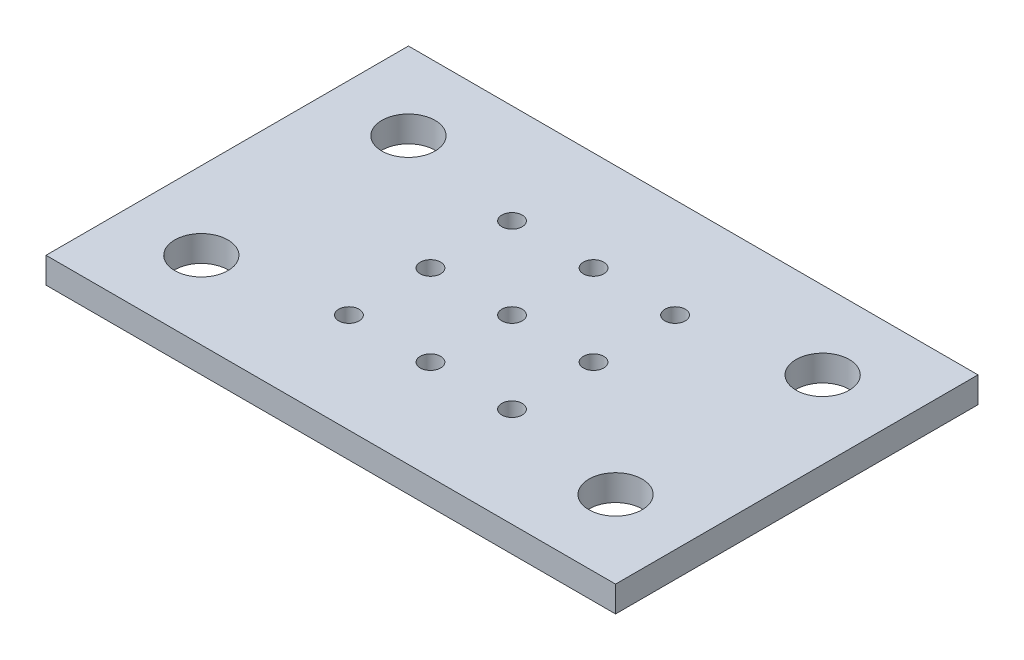
SolidWorks part; units mm, degrees
ref_plane "Front Plane" through (0, 0, 0) normal (0, 0, 1) x (1, 0, 0)
ref_plane "Top Plane" through (0, 0, 0) normal (0, 1, 0) x (1, 0, 0)
ref_plane "Right Plane" through (0, 0, 0) normal (1, 0, 0) x (0, 0, -1)
sketch "Sketch1" plane through (0, 0, 0) normal (0, 1, 0) x (1, 0, 0)
  line L0 (9.525, 34.925) -> (0, 34.925) construction
  line L1 (0, 0) -> (69.85, 0)
  line L2 (0, 0) -> (0, 44.45)
  line L3 (0, 44.45) -> (69.85, 44.45)
  line L4 (69.85, 0) -> (69.85, 44.45)
  line L5 (9.525, 34.925) -> (60.325, 34.925) construction
  line L6 (9.525, 34.925) -> (9.525, 9.525) construction
  line L7 (9.525, 9.525) -> (60.325, 9.525) construction
  line L8 (60.325, 34.925) -> (60.325, 9.525) construction
  line L9 (9.525, 34.925) -> (9.525, 44.45) construction
  line L10 (34.925, 22.225) -> (34.925, 32.225) construction
  circle A0 centre (9.525, 34.925) radius 3.2639
  circle A1 centre (60.325, 34.925) radius 3.2639
  circle A2 centre (9.525, 9.525) radius 3.2639
  circle A3 centre (60.325, 9.525) radius 3.2639
  circle A4 centre (34.925, 22.225) radius 1.25
  circle A5 centre (44.925, 22.225) radius 1.25
  circle A6 centre (44.925, 32.225) radius 1.25
  circle A7 centre (34.925, 32.225) radius 1.25
  circle A8 centre (24.925, 22.225) radius 1.25
  circle A9 centre (24.925, 32.225) radius 1.25
  circle A10 centre (34.925, 32.225) radius 1.25
  circle A11 centre (44.925, 22.225) radius 1.25
  circle A12 centre (44.925, 12.225) radius 1.25
  circle A13 centre (34.925, 12.225) radius 1.25
  circle A14 centre (24.925, 22.225) radius 1.25
  circle A15 centre (24.925, 12.225) radius 1.25
  circle A16 centre (34.925, 12.225) radius 1.25
  point P13 (34.925, 34.925)
  point P14 (34.925, 44.45)
  point P20 (69.85, 22.225)
  dimension "D5" = 6.5278
  dimension "D6" = 2.5
  dimension "D1" = 69.85
  dimension "D2" = 44.45
  dimension "D3" = 50.8
  dimension "D4" = 25.4
  dimension "D9" = 10
  dimension "D16" = 10
  dimension "D17" = 10
  dimension "D18" = 10
  dimension "D19" = 10
  dimension "D20" = 10
  dimension "D21" = 10
  dimension "D22" = 10
  dimension "D7" = 2
  dimension "D8" = 2
  dimension "D10" = 2
  dimension "D11" = 2
  dimension "D12" = 2
  dimension "D13" = 2
  dimension "D14" = 2
  dimension "D15" = 2
extrude "Boss-Extrude1" add sketch "Sketch1" along normal blind 3.175 contours L1 L4 L3 L2 A15 A13 A12 A9 A8 A7 A6 A5 A4 A3 A2 A1 A0
